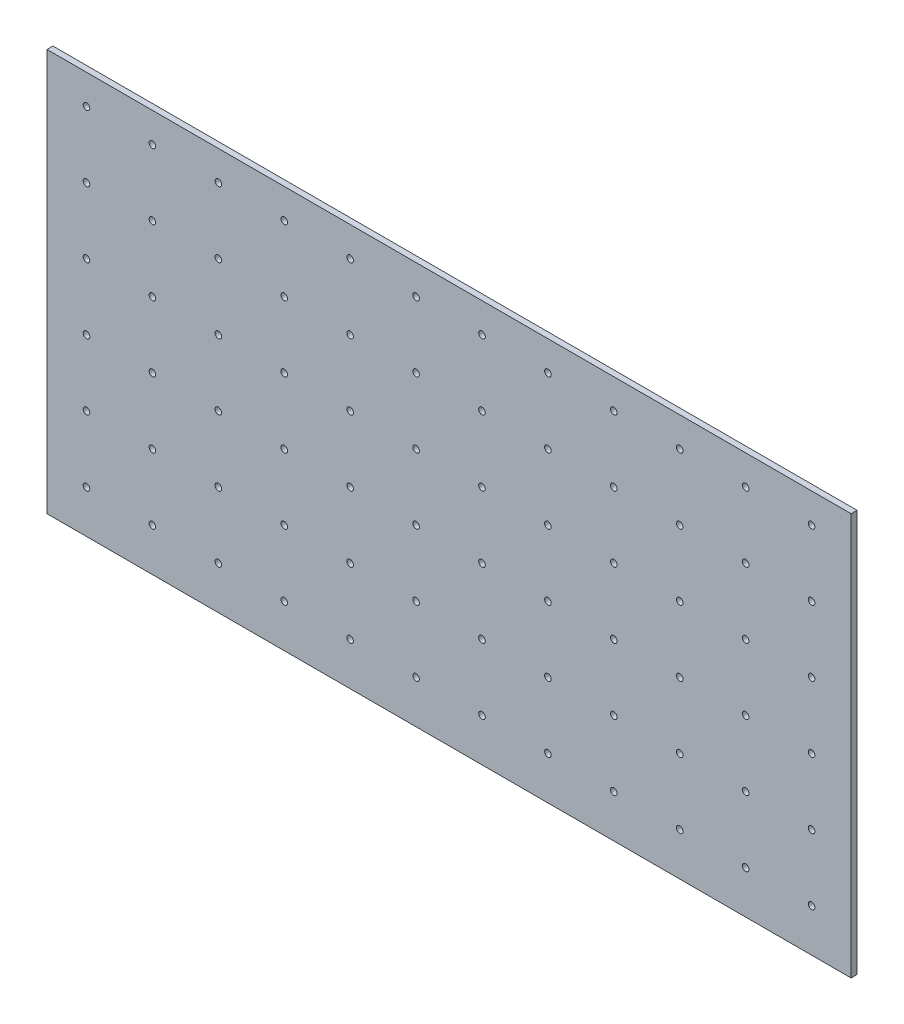
SolidWorks part; units mm, degrees
ref_plane "Front Plane" through (0, 0, 0) normal (0, 0, 1) x (1, 0, 0)
ref_plane "Top Plane" through (0, 0, 0) normal (0, 1, 0) x (1, 0, 0)
ref_plane "Right Plane" through (0, 0, 0) normal (1, 0, 0) x (0, 0, -1)
sketch "Sketch1" plane through (0, 0, 0) normal (0, 0, 1) x (1, 0, 0)
  line L1 (-2210.892, -618.5915) -> (229.108, -618.5915)
  line L2 (-2210.892, -618.5915) -> (-2210.892, 601.4085)
  line L3 (-2210.892, 601.4085) -> (229.108, 601.4085)
  line L4 (229.108, -618.5915) -> (229.108, 601.4085)
  circle A0 centre (-2090.892, 511.4085) radius 10
  circle A1 centre (-1890.892, 511.4085) radius 10
  circle A2 centre (-1690.892, 511.4085) radius 10
  circle A3 centre (-1490.892, 511.4085) radius 10
  circle A4 centre (-2090.892, 311.4085) radius 10
  circle A5 centre (-1890.892, 311.4085) radius 10
  circle A6 centre (-1690.892, 311.4085) radius 10
  circle A7 centre (-1490.892, 311.4085) radius 10
  circle A8 centre (-1290.892, 511.4085) radius 10
  circle A9 centre (-1290.892, 311.4085) radius 10
  circle A10 centre (-1090.892, 511.4085) radius 10
  circle A11 centre (-1090.892, 311.4085) radius 10
  circle A12 centre (-890.892, 511.4085) radius 10
  circle A13 centre (-890.892, 311.4085) radius 10
  circle A14 centre (-890.892, 111.4085) radius 10
  circle A15 centre (-1090.892, 111.4085) radius 10
  circle A16 centre (-1290.892, 111.4085) radius 10
  circle A17 centre (-1490.892, 111.4085) radius 10
  circle A18 centre (-1690.892, 111.4085) radius 10
  circle A19 centre (-1890.892, 111.4085) radius 10
  circle A20 centre (-2090.892, 111.4085) radius 10
  circle A21 centre (-2090.892, -88.5915) radius 10
  circle A22 centre (-1890.892, -88.5915) radius 10
  circle A23 centre (-1690.892, -88.5915) radius 10
  circle A24 centre (-1490.892, -88.5915) radius 10
  circle A25 centre (-1290.892, -88.5915) radius 10
  circle A26 centre (-1090.892, -88.5915) radius 10
  circle A27 centre (-890.892, -88.5915) radius 10
  circle A28 centre (-690.892, -88.5915) radius 10
  circle A29 centre (-490.892, -88.5915) radius 10
  circle A30 centre (-490.892, 111.4085) radius 10
  circle A31 centre (-490.892, 311.4085) radius 10
  circle A32 centre (-490.892, 511.4085) radius 10
  circle A33 centre (-690.892, 511.4085) radius 10
  circle A34 centre (-690.892, 311.4085) radius 10
  circle A35 centre (-690.892, 111.4085) radius 10
  circle A36 centre (-490.892, -288.5915) radius 10
  circle A37 centre (-690.892, -288.5915) radius 10
  circle A38 centre (-890.892, -288.5915) radius 10
  circle A39 centre (-1090.892, -288.5915) radius 10
  circle A40 centre (-1290.892, -288.5915) radius 10
  circle A41 centre (-1490.892, -288.5915) radius 10
  circle A42 centre (-1690.892, -288.5915) radius 10
  circle A43 centre (-1890.892, -288.5915) radius 10
  circle A44 centre (-2090.892, -288.5915) radius 10
  circle A45 centre (-2090.892, -488.5915) radius 10
  circle A46 centre (-1890.892, -488.5915) radius 10
  circle A47 centre (-1690.892, -488.5915) radius 10
  circle A48 centre (-1490.892, -488.5915) radius 10
  circle A49 centre (-1290.892, -488.5915) radius 10
  circle A50 centre (-1090.892, -488.5915) radius 10
  circle A51 centre (-890.892, -488.5915) radius 10
  circle A52 centre (-690.892, -488.5915) radius 10
  circle A53 centre (-490.892, -488.5915) radius 10
  circle A54 centre (-290.892, 511.4085) radius 10
  circle A55 centre (-290.892, 311.4085) radius 10
  circle A56 centre (-290.892, 111.4085) radius 10
  circle A57 centre (-290.892, -88.5915) radius 10
  circle A58 centre (-290.892, -288.5915) radius 10
  circle A59 centre (-290.892, -488.5915) radius 10
  circle A60 centre (-90.892, 511.4085) radius 10
  circle A61 centre (-90.892, 311.4085) radius 10
  circle A62 centre (-90.892, 111.4085) radius 10
  circle A63 centre (-90.892, -88.5915) radius 10
  circle A64 centre (-90.892, -288.5915) radius 10
  circle A65 centre (-90.892, -488.5915) radius 10
  circle A66 centre (109.108, -488.5915) radius 10
  circle A67 centre (109.108, -288.5915) radius 10
  circle A68 centre (109.108, -88.5915) radius 10
  circle A69 centre (109.108, 111.4085) radius 10
  circle A70 centre (109.108, 311.4085) radius 10
  circle A71 centre (109.108, 511.4085) radius 10
  point P40 (-2090.892, 511.4085)
  point P41 (-1890.892, 511.4085)
  point P42 (-1690.892, 511.4085)
  point P43 (-1490.892, 511.4085)
  point P44 (-1290.892, 511.4085)
  point P45 (-1090.892, 511.4085)
  point P46 (-2090.892, 311.4085)
  point P47 (-1890.892, 311.4085)
  point P48 (-1690.892, 311.4085)
  point P49 (-1490.892, 311.4085)
  point P50 (-1290.892, 311.4085)
  point P51 (-1090.892, 311.4085)
  point P52 (-1090.892, 111.4085)
  point P53 (-1290.892, 111.4085)
  point P54 (-1490.892, 111.4085)
  point P55 (-1690.892, 111.4085)
  point P56 (-1890.892, 111.4085)
  point P57 (-2090.892, 111.4085)
  point P58 (-890.892, 311.4085)
  point P59 (-890.892, 111.4085)
  point P60 (-890.892, 511.4085)
  point P61 (-690.892, 511.4085)
  point P62 (-490.892, 511.4085)
  point P63 (-290.892, 511.4085)
  point P64 (-90.892, 511.4085)
  point P65 (109.108, 511.4085)
  point P66 (109.108, 311.4085)
  point P67 (-90.892, 311.4085)
  point P68 (-290.892, 311.4085)
  point P69 (-490.892, 311.4085)
  point P70 (-690.892, 311.4085)
  point P71 (-690.892, 111.4085)
  point P72 (-490.892, 111.4085)
  point P73 (-290.892, 111.4085)
  point P74 (-90.892, 111.4085)
  point P75 (109.108, 111.4085)
  point P76 (109.108, -88.5915)
  point P77 (-90.892, -88.5915)
  point P78 (-290.892, -88.5915)
  point P79 (-490.892, -88.5915)
  point P80 (-690.892, -88.5915)
  point P81 (-890.892, -88.5915)
  point P82 (-890.892, -288.5915)
  point P83 (-690.892, -288.5915)
  point P84 (-490.892, -288.5915)
  point P85 (-290.892, -288.5915)
  point P86 (-90.892, -288.5915)
  point P87 (109.108, -288.5915)
  point P88 (109.108, -488.5915)
  point P89 (-90.892, -488.5915)
  point P90 (-290.892, -488.5915)
  point P91 (-490.892, -488.5915)
  point P92 (-690.892, -488.5915)
  point P93 (-890.892, -488.5915)
  point P94 (-1090.892, -488.5915)
  point P95 (-1090.892, -288.5915)
  point P96 (-1090.892, -88.5915)
  point P97 (-1290.892, -88.5915)
  point P98 (-1290.892, -288.5915)
  point P99 (-1290.892, -488.5915)
  point P100 (-1490.892, -488.5915)
  point P101 (-1490.892, -288.5915)
  point P102 (-1490.892, -88.5915)
  point P103 (-1690.892, -488.5915)
  point P104 (-1690.892, -288.5915)
  point P105 (-1890.892, -488.5915)
  point P106 (-1890.892, -288.5915)
  point P107 (-1690.892, -88.5915)
  point P108 (-1890.892, -88.5915)
  point P109 (-2090.892, -88.5915)
  point P110 (-2090.892, -288.5915)
  point P111 (-2090.892, -488.5915)
  dimension "D1" = 2440
  dimension "D2" = 1220
extrude "Boss-Extrude2" add sketch "Sketch1" along normal blind 18
